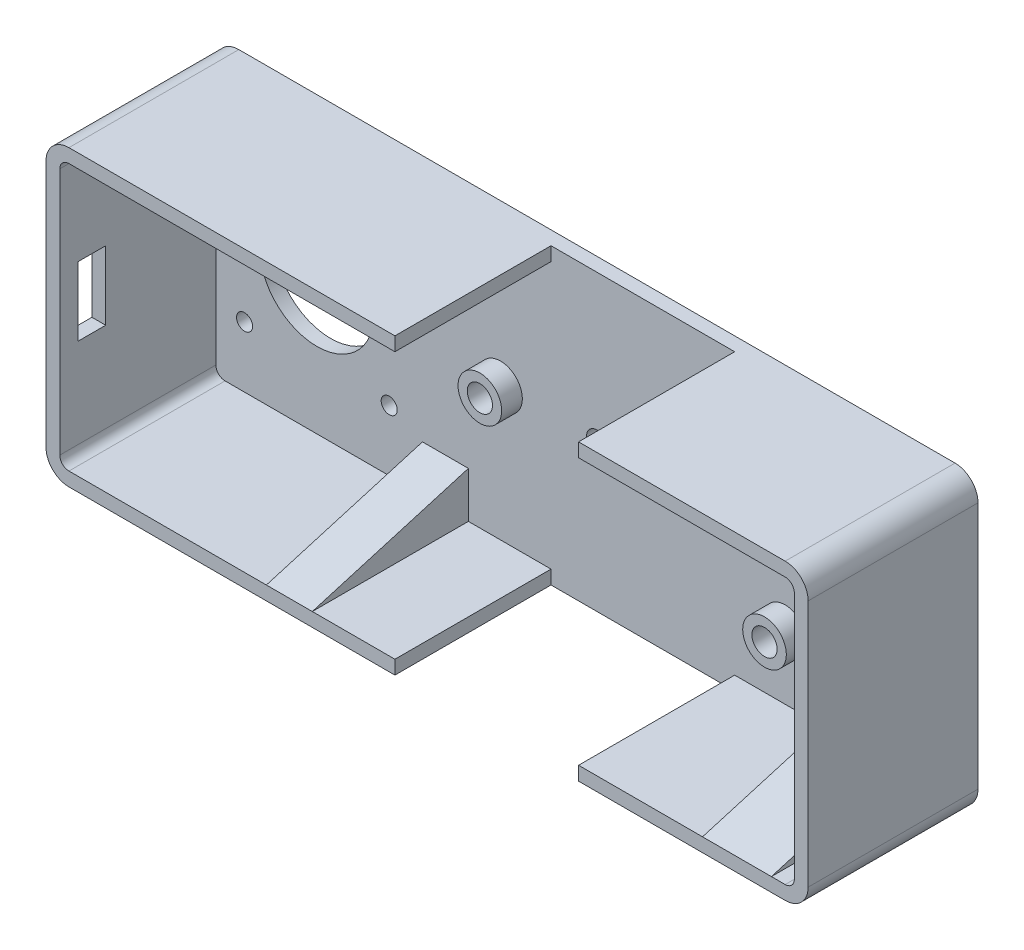
SolidWorks part; units mm, degrees
ref_plane "Front Plane" through (0, 0, 0) normal (0, 0, 1) x (1, 0, 0)
ref_plane "Top Plane" through (0, 0, 0) normal (0, 1, 0) x (1, 0, 0)
ref_plane "Right Plane" through (0, 0, 0) normal (1, 0, 0) x (0, 0, -1)
sketch "Sketch1" plane through (0, 0, 0) normal (0, 0, 1) x (1, 0, 0)
  line L1 (-78, 32) -> (78, 32)
  line L2 (-83, 27) -> (-83, -27)
  line L3 (-78, -32) -> (78, -32)
  line L4 (83, 27) -> (83, -27)
  line L5 (-83, 32) -> (83, -32) construction
  line L6 (-83, -32) -> (83, 32) construction
  arc A0 (78, -32) -> (83, -27) centre (78, -27) ccw
  arc A1 (78, 32) -> (83, 27) centre (78, 27) cw
  arc A2 (-83, -27) -> (-78, -32) centre (-78, -27) ccw
  arc A3 (-78, 32) -> (-83, 27) centre (-78, 27) ccw
  point P0 (0, 0)
  dimension "D3" = 5
  dimension "D1" = 64
  dimension "D2" = 166
extrude "Boss-Extrude1" add sketch "Sketch1" along normal blind 37
sketch "Sketch2" plane through (0, 0, 37) normal (0, 0, 1) x (1, 0, 0)
  line L0 (-58, 0) -> (0, 0) construction
  line L1 (-42.25, 15.75) -> (-73.75, 15.75) construction
  line L2 (-42.25, 15.75) -> (-42.25, -15.75) construction
  line L3 (-42.25, -15.75) -> (-73.75, -15.75) construction
  line L4 (-73.75, 15.75) -> (-73.75, -15.75) construction
  line L5 (-42.25, 15.75) -> (-73.75, -15.75) construction
  line L6 (-42.25, -15.75) -> (-73.75, 15.75) construction
  line L7 (-83, 27) -> (-83, -27) construction
  line L8 (44, 15) -> (44, -15) construction
  line L9 (0, 0) -> (44, 0) construction
  line L10 (44, 0) -> (64, 0) construction
  circle A0 centre (-73.75, 15.75) radius 1.75
  circle A1 centre (-42.25, 15.75) radius 1.75
  circle A2 centre (-73.75, -15.75) radius 1.75
  circle A3 centre (-42.25, -15.75) radius 1.75
  circle A4 centre (-58, 0) radius 12.5
  circle A5 centre (44, 15) radius 2.75
  circle A6 centre (44, -15) radius 2.75
  circle A7 centre (-18, 0) radius 2.75
  circle A8 centre (64, 0) radius 2.25
  point P0 (-58, 0)
  dimension "D1" = 3.5
  dimension "D4" = 25
  dimension "D5" = 5.5
  dimension "D10" = 4.5
  dimension "D2" = 31.5
  dimension "D3" = 25
  dimension "D6" = 30
  dimension "D7" = 127
  dimension "D8" = 62
  dimension "D9" = 20
extrude "Cut-Extrude1" cut sketch "Sketch2" against normal through all
sketch "Sketch3" plane through (0, 0, 37) normal (0, 0, 1) x (1, 0, 0)
  circle A3 centre (44, 15) radius 2.75 construction
  circle A4 centre (44, 15) radius 2.75
  circle A5 centre (44, 15) radius 4.75
  circle A6 centre (-18, 0) radius 2.75 construction
  circle A7 centre (44, -15) radius 2.75 construction
  circle A8 centre (-18, 0) radius 2.75
  circle A9 centre (44, -15) radius 2.75
  circle A10 centre (-18, 0) radius 4.75
  circle A11 centre (44, -15) radius 4.75
  dimension "D1" = 2
  dimension "D2" = 2
sketch "Sketch4" plane through (0, 0, 0) normal (0, 0, 1) x (1, 0, 0)
  line L0 (83, 10) -> (83, -10)
  line L1 (83, -27) -> (83, 27) construction
  line L2 (0, 0) -> (83, 0) construction
  line L3 (83, 10) -> (93, 10)
  line L4 (83, -10) -> (93, -10)
  line L5 (93, 10) -> (93, -10) construction
  arc A0 (93, -10) -> (93, 10) centre (93, 0) ccw
  circle A1 centre (93, 0) radius 2.25
  dimension "D3" = 4.5
  dimension "D1" = 20
  dimension "D2" = 10
sketch "Sketch5" plane through (0, 0, 37) normal (0, 0, 1) x (1, 0, 0)
  line L0 (-18, 0) -> (44, 0) construction
  line L1 (44, 0) -> (44, -15) construction
  circle A0 centre (3, 0) radius 2.25
  circle A1 centre (23, 0) radius 2.25
  point P10 (13, 0)
  dimension "D3" = 4.5
  dimension "D1" = 10
  dimension "D2" = 10
extrude "Cut-Extrude2" cut sketch "Sketch5" against normal through all
sketch "Sketch6" plane through (0, 0, 37) normal (0, 0, 1) x (1, 0, 0)
  line L0 (78, 32) -> (-78, 32) construction
  line L1 (-78, -29) -> (78, -29)
  line L2 (-80, -27) -> (-80, 27)
  line L3 (-78, 29) -> (78, 29)
  line L4 (80, -27) -> (80, 27)
  line L5 (-80, -29) -> (80, 29) construction
  line L6 (-80, 29) -> (80, -29) construction
  line L7 (83, -27) -> (83, 27) construction
  arc A0 (-80, 27) -> (-78, 29) centre (-78, 27) cw
  arc A1 (-78, -29) -> (-80, -27) centre (-78, -27) cw
  arc A2 (78, -29) -> (80, -27) centre (78, -27) ccw
  arc A3 (78, 29) -> (80, 27) centre (78, 27) cw
  point P0 (0, 0)
  dimension "D3" = 2
  dimension "D1" = 3
  dimension "D2" = 3
extrude "Cut-Extrude3" cut sketch "Sketch6" against normal blind 34
sketch "Sketch7" plane through (0, 0, 3) normal (0, 0, 1) x (1, 0, 0)
  circle A0 centre (-18, 0) radius 4.75
  circle A1 centre (-18, 0) radius 2.75 construction
  circle A2 centre (44, -15) radius 4.75
  circle A3 centre (44, 15) radius 4.75
  circle A4 centre (44, -15) radius 2.75 construction
  dimension "D1" = 2
  dimension "D2" = 2
  dimension "D3" = 9.5
extrude "Boss-Extrude2" add sketch "Sketch7" along normal blind 4.5
sketch "Sketch10" plane through (0, 0, 37) normal (0, 0, 1) x (1, 0, 0)
  line L0 (-78, -32) -> (78, -32) construction
  line L1 (-7, -32) -> (33, -32)
  line L2 (-7, -32) -> (-7, 32)
  line L3 (-7, 32) -> (33, 32)
  line L4 (33, -32) -> (33, 32)
  line L5 (-7, -32) -> (33, 32) construction
  line L6 (-7, 32) -> (33, -32) construction
  line L7 (78, 32) -> (-78, 32) construction
  line L8 (13, 0) -> (44, 0) construction
  line L9 (0, 0) -> (83, 0) construction
  line L10 (44, 0) -> (44, -15) construction
  point P0 (13, 0)
  dimension "D1" = 40
  dimension "D2" = 31
extrude "Cut-Extrude4" cut sketch "Sketch10" against normal blind 34
sketch "Sketch11" plane through (0, 0, 7.5) normal (0, 0, 1) x (1, 0, 0)
  circle A0 centre (44, -15) radius 2.75
  circle A1 centre (-18, 0) radius 2.75
  circle A2 centre (44, 15) radius 2.75
  dimension "D1" = 5.5
  dimension "D2" = 5.5
  dimension "D3" = 5.5
extrude "Cut-Extrude5" cut sketch "Sketch11" against normal through all
sketch "Sketch12" plane through (0, 0, 3) normal (0, 0, 1) x (1, 0, 0)
  line L0 (33, -29) -> (78, -29) construction
  line L1 (60, -29) -> (75, -29)
  line L2 (60, -29) -> (60, -19)
  line L3 (60, -19) -> (75, -19)
  line L4 (75, -29) -> (75, -19)
  line L5 (83, 0) -> (32.1507, 0) construction
  line L6 (0, 0) -> (83, 0) construction
  line L7 (60, 19) -> (75, 19)
  line L8 (75, 29) -> (75, 19)
  line L9 (60, 29) -> (75, 29)
  line L10 (60, 29) -> (60, 19)
  line L11 (80, -27) -> (80, 27) construction
  line L12 (80, -6) -> (60, -6)
  line L13 (80, -6) -> (80, -16)
  line L14 (80, -16) -> (60, -16)
  line L15 (60, -6) -> (60, -16)
  line L16 (80, 16) -> (60, 16)
  line L17 (60, 6) -> (60, 16)
  line L18 (80, 6) -> (60, 6)
  line L19 (80, 6) -> (80, 16)
  line L20 (80, -27) -> (80, 27) construction
  line L21 (-78, -29) -> (-7, -29) construction
  line L22 (-35, -29) -> (-25, -29)
  line L23 (-35, -29) -> (-35, -19)
  line L24 (-35, -19) -> (-25, -19)
  line L25 (-25, -29) -> (-25, -19)
  line L26 (-35, 19) -> (-25, 19)
  line L27 (-25, 29) -> (-25, 19)
  line L28 (-35, 29) -> (-25, 29)
  line L29 (-35, 29) -> (-35, 19)
  line L30 (-80, 27) -> (-80, -27) construction
  dimension "D1" = 15
  dimension "D2" = 5
  dimension "D3" = 10
  dimension "D4" = 20
  dimension "D5" = 3
  dimension "D6" = 10
  dimension "D7" = 10
  dimension "D8" = 10
  dimension "D9" = 45
extrude "Boss-Extrude3" add sketch "Sketch12" along normal through all
sketch "Sketch14" plane through (0, -16, 0) normal (0, -1, 0) x (1, 0, 0)
  line L3 (80, 37) -> (60, 37)
  line L4 (60, 37) -> (60, 3)
  line L5 (60, 3) -> (80, 37)
  dimension "D1" = 34
extrude "Cut-Extrude6" cut sketch "Sketch14" against normal blind 33
sketch "Sketch16" plane through (75, 0, 0) normal (1, 0, 0) x (0, 0, -1)
  line L0 (-37, -19) -> (-3, -19)
  line L1 (-3, -19) -> (-37, -29)
  line L2 (-37, -27) -> (-37, 27) construction
  line L3 (-37, -29) -> (-37, -19)
  dimension "D1" = 10
  dimension "D2" = 34
extrude "Cut-Extrude8" cut sketch "Sketch16" against normal blind 15
sketch "Sketch17" plane through (60, 0, 0) normal (-1, 0, 0) x (0, 0, 1)
  line L6 (37, 19) -> (3, 19)
  line L7 (3, 19) -> (37, 29)
  line L8 (37, 29) -> (37, 19)
extrude "Cut-Extrude9" cut sketch "Sketch17" against normal blind 15
sketch "Sketch18" plane through (-25, 0, 0) normal (1, 0, 0) x (0, 0, -1)
  line L0 (-37, -29) -> (-37, -19)
  line L1 (-37, -19) -> (-3, -19)
  line L2 (-3, -19) -> (-37, -29)
extrude "Cut-Extrude10" cut sketch "Sketch18" against normal blind 10
sketch "Sketch19" plane through (-25, 0, 0) normal (1, 0, 0) x (0, 0, -1)
  line L0 (-37, 29) -> (-3, 19)
  line L1 (-3, 19) -> (-37, 19)
  line L2 (-37, 19) -> (-37, 29)
extrude "Cut-Extrude11" cut sketch "Sketch19" against normal blind 10
sketch "Sketch20" plane through (-83, 0, 0) normal (-1, 0, 0) x (0, 0, 1)
  line L0 (37, 27) -> (37, -27) construction
  line L1 (33, 7.5) -> (27, 7.5)
  line L2 (33, 7.5) -> (33, -7.5)
  line L3 (33, -7.5) -> (27, -7.5)
  line L4 (27, 7.5) -> (27, -7.5)
  line L5 (33, 7.5) -> (27, -7.5) construction
  line L6 (33, -7.5) -> (27, 7.5) construction
  line L7 (0, 0) -> (37, 0) construction
  line L8 (37, -2.75) -> (37, 2.75) construction
  point P0 (30, 0)
  point P12 (0, 0)
  dimension "D1" = 4
  dimension "D2" = 15
  dimension "D3" = 6
extrude "Cut-Extrude12" cut sketch "Sketch20" against normal blind 3
